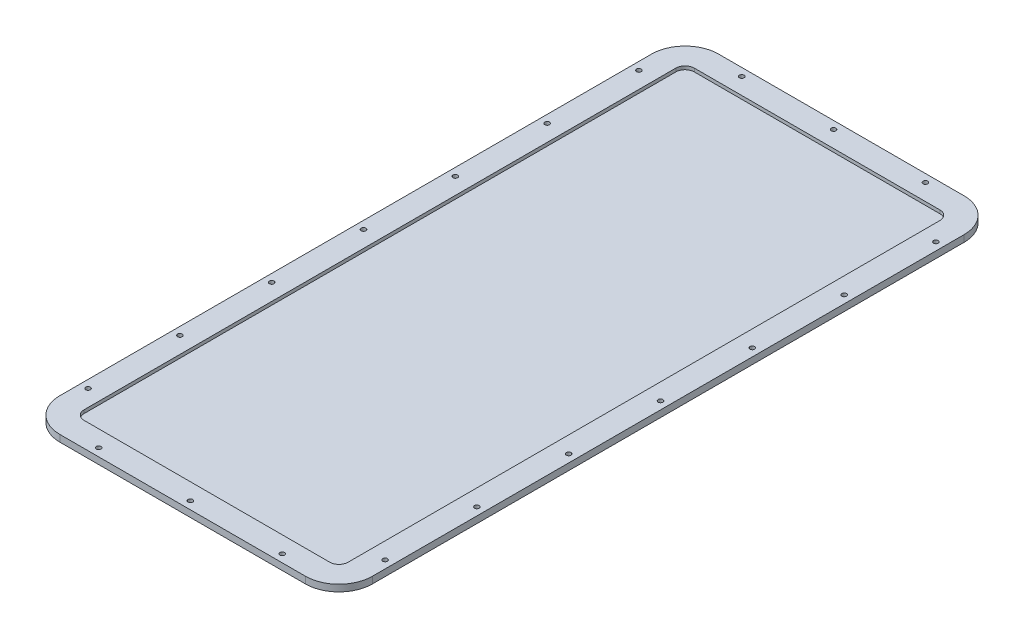
SolidWorks part; units mm, degrees
material "6061 Alloy"
ref_plane "Front Plane" through (0, 0, 0) normal (0, 0, 1) x (1, 0, 0)
ref_plane "Top Plane" through (0, 0, 0) normal (0, 1, 0) x (1, 0, 0)
ref_plane "Right Plane" through (0, 0, 0) normal (1, 0, 0) x (0, 0, -1)
sketch "Sketch1" plane through (0, 0, 0) normal (0, 1, 0) x (-1, 0, 0)
  line L8 (90.9274, 302.9312) -> (-129.0726, 302.9312)
  line L9 (-159.0726, 272.9312) -> (-159.0726, -257.0688)
  line L10 (-129.0726, -287.0688) -> (90.9274, -287.0688)
  line L11 (120.9274, -257.0688) -> (120.9274, 272.9312)
  arc A8 (-129.0726, 302.9312) -> (-159.0726, 272.9312) centre (-129.0726, 272.9312) ccw
  arc A9 (-159.0726, -257.0688) -> (-129.0726, -287.0688) centre (-129.0726, -257.0688) ccw
  arc A10 (90.9274, -287.0688) -> (120.9274, -257.0688) centre (90.9274, -257.0688) ccw
  arc A11 (120.9274, 272.9312) -> (90.9274, 302.9312) centre (90.9274, 272.9312) ccw
  circle A19 centre (-152.0726, 254.6082) radius 2.1
  circle A20 centre (-101.2983, 295.9312) radius 2.1
  circle A21 centre (-19.0726, 295.9312) radius 2.1
  circle A22 centre (63.1531, 295.9312) radius 2.1
  circle A23 centre (113.9274, 254.6082) radius 2.1
  circle A39 centre (-152.0726, 7.9312) radius 2.1
  circle A40 centre (-152.0726, -74.2945) radius 2.1
  circle A41 centre (-152.0726, -156.5202) radius 2.1
  circle A42 centre (-152.0726, -238.7458) radius 2.1
  circle A43 centre (-101.2983, -280.0688) radius 2.1
  circle A44 centre (-19.0726, -280.0688) radius 2.1
  circle A45 centre (63.1531, -280.0688) radius 2.1
  circle A46 centre (113.9274, -238.7458) radius 2.1
  circle A47 centre (113.9274, -156.5202) radius 2.1
  circle A48 centre (113.9274, -74.2945) radius 2.1
  circle A49 centre (113.9274, 7.9312) radius 2.1
  circle A50 centre (-152.0726, 90.1568) radius 2.1
  circle A51 centre (-152.0726, 172.3825) radius 2.1
  circle A52 centre (113.9274, 90.1568) radius 2.1
  circle A53 centre (113.9274, 172.3825) radius 2.1
  dimension "D1" = 220
  dimension "D2" = 4.2
  dimension "D3" = 530
extrude "Boss-Extrude1" add sketch "Sketch1" along normal blind 6
sketch "Sketch3" plane through (0, 6, 0) normal (0, 1, 0) x (1, 0, 0)
  line L0 (19.0726, -302.9312) -> (19.0726, 329.2915) construction
  line L1 (129.0726, -281.1812) -> (-90.9274, -281.1812)
  line L2 (137.3226, -272.9312) -> (137.3226, 257.0688)
  line L3 (129.0726, 265.3188) -> (-90.9274, 265.3188)
  line L4 (-99.1774, -272.9312) -> (-99.1774, 257.0688)
  line L5 (-90.9274, -302.9312) -> (129.0726, -302.9312) construction
  line L6 (159.0726, -7.9312) -> (-213.7716, -7.9312) construction
  line L7 (159.0726, -272.9312) -> (159.0726, 257.0688) construction
  arc A0 (137.3226, 257.0688) -> (129.0726, 265.3188) centre (129.0726, 257.0688) ccw
  arc A1 (-90.9274, 265.3188) -> (-99.1774, 257.0688) centre (-90.9274, 257.0688) ccw
  arc A2 (-90.9274, -281.1812) -> (-99.1774, -272.9312) centre (-90.9274, -272.9312) cw
  arc A3 (129.0726, -281.1812) -> (137.3226, -272.9312) centre (129.0726, -272.9312) ccw
  point P14 (137.3226, 265.3188)
  point P19 (-99.1774, -281.1812)
  point P22 (137.3226, -281.1812)
  dimension "D3" = 8.25
  dimension "D1" = 546.5
  dimension "D2" = 236.5
extrude "Cut-Extrude1" cut sketch "Sketch3" against normal blind 3
sketch "Sketch4" plane through (0, 0, 0) normal (0, -1, 0) x (1, 0, 0)
  circle A0 centre (101.2983, -280.0688) radius 4.125
  circle A1 centre (152.0726, -238.7458) radius 4.125
  circle A2 centre (19.0726, -280.0688) radius 4.125
  circle A3 centre (-63.1531, -280.0688) radius 4.125
  circle A4 centre (-113.9274, -238.7458) radius 4.125
  circle A5 centre (-113.9274, -156.5202) radius 4.125
  circle A6 centre (-113.9274, -74.2945) radius 4.125
  circle A7 centre (-113.9274, 7.9312) radius 4.125
  circle A8 centre (-113.9274, 90.1568) radius 4.125
  circle A9 centre (-113.9274, 172.3825) radius 4.125
  circle A10 centre (-113.9274, 254.6082) radius 4.125
  circle A11 centre (-63.1531, 295.9312) radius 4.125
  circle A12 centre (19.0726, 295.9312) radius 4.125
  circle A13 centre (101.2983, 295.9312) radius 4.125
  circle A14 centre (152.0726, 254.6082) radius 4.125
  circle A15 centre (152.0726, 172.3825) radius 4.125
  circle A16 centre (152.0726, 90.1568) radius 4.125
  circle A17 centre (152.0726, 7.9312) radius 4.125
  circle A18 centre (152.0726, -74.2945) radius 4.125
  circle A19 centre (152.0726, -156.5202) radius 4.125
  point P59 (152.0726, 7.9312)
  dimension "D1" = 8.25
extrude "Cut-Extrude2" cut sketch "Sketch4" against normal blind 2.5
sketch "Plate Dims" plane through (0, 3, 0) normal (0, 1, 0) x (1, 0, 0)
  line L4 (129.0726, 265.3188) -> (-90.9274, 265.3188)
  line L5 (-99.1774, 257.0688) -> (-99.1774, -272.9312)
  line L6 (-90.9274, -281.1812) -> (129.0726, -281.1812)
  line L7 (137.3226, -272.9312) -> (137.3226, 257.0688)
  line L8 (129.0726, 265.3188) -> (-90.9274, 265.3188)
  line L9 (-99.1774, 257.0688) -> (-99.1774, -272.9312)
  line L10 (-90.9274, -281.1812) -> (129.0726, -281.1812)
  line L11 (137.3226, -272.9312) -> (137.3226, 257.0688)
  arc A4 (137.3226, 257.0688) -> (129.0726, 265.3188) centre (129.0726, 257.0688) ccw
  arc A5 (-90.9274, 265.3188) -> (-99.1774, 257.0688) centre (-90.9274, 257.0688) ccw
  arc A6 (-99.1774, -272.9312) -> (-90.9274, -281.1812) centre (-90.9274, -272.9312) ccw
  arc A7 (129.0726, -281.1812) -> (137.3226, -272.9312) centre (129.0726, -272.9312) ccw
  arc A8 (137.3226, 257.0688) -> (129.0726, 265.3188) centre (129.0726, 257.0688) ccw
  arc A9 (-90.9274, 265.3188) -> (-99.1774, 257.0688) centre (-90.9274, 257.0688) ccw
  arc A10 (-99.1774, -272.9312) -> (-90.9274, -281.1812) centre (-90.9274, -272.9312) ccw
  arc A11 (129.0726, -281.1812) -> (137.3226, -272.9312) centre (129.0726, -272.9312) ccw
  dimension "D1" = 0
